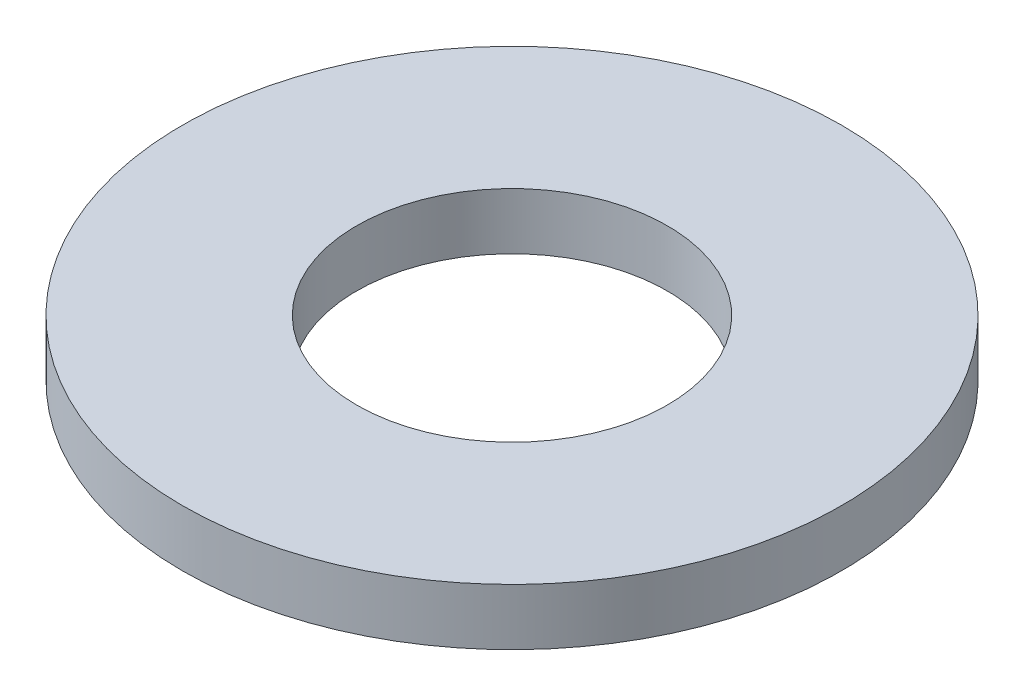
SolidWorks part; units mm, degrees
ref_plane "Front Plane" through (0, 0, 0) normal (0, 0, 1) x (1, 0, 0)
ref_plane "Top Plane" through (0, 0, 0) normal (0, 1, 0) x (1, 0, 0)
ref_plane "Right Plane" through (0, 0, 0) normal (1, 0, 0) x (0, 0, -1)
sketch "Sketch1" plane through (0, 0, 0) normal (0, 1, 0) x (1, 0, 0)
  circle A0 centre (0, 0) radius 3.5
  circle A1 centre (0, 0) radius 1.65
  dimension "D1" = 7
  dimension "D2" = 3.3
extrude "Boss-Extrude1" add sketch "Sketch1" along normal blind 0.6
